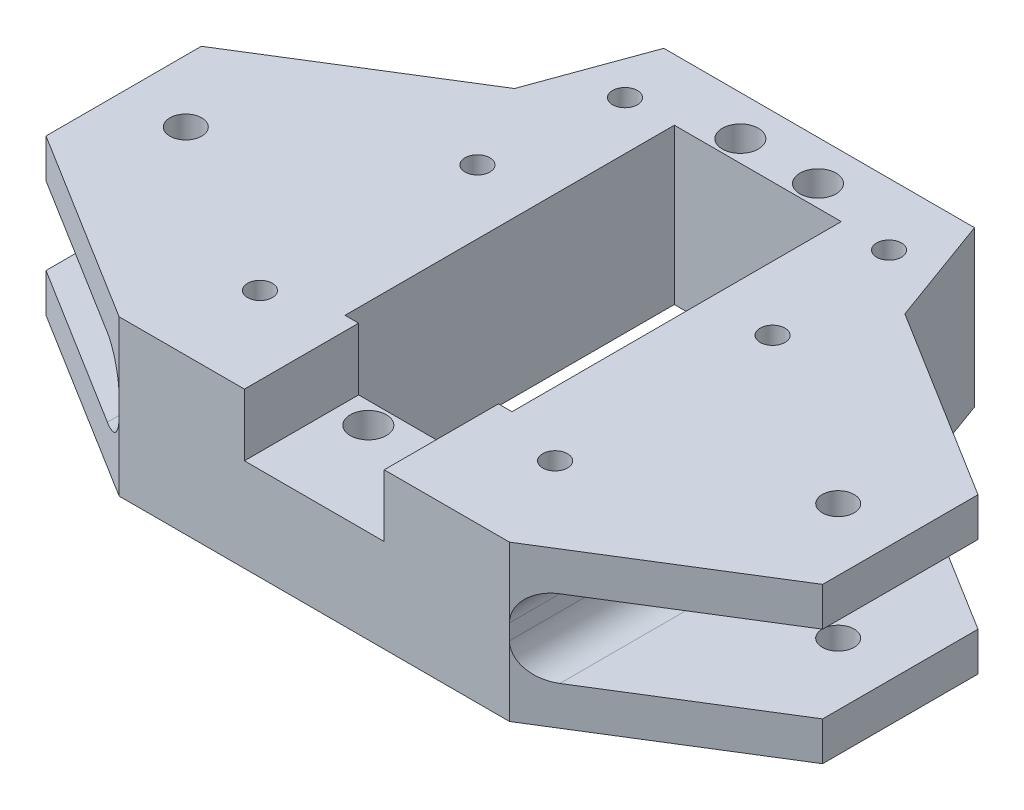
SolidWorks part; units mm, degrees
ref_plane "Front Plane" through (0, 0, 0) normal (0, 0, 1) x (1, 0, 0)
ref_plane "Top Plane" through (0, 0, 0) normal (0, 1, 0) x (1, 0, 0)
ref_plane "Right Plane" through (0, 0, 0) normal (1, 0, 0) x (0, 0, -1)
sketch "Sketch1" plane through (0, 0, 0) normal (0, 1, 0) x (1, 0, 0)
  line L0 (0, 0) -> (0, 55585.7092) construction
  line L1 (0, 0) -> (55585.7092, 0) construction
  line L2 (20, 39.5477) -> (-20, 39.5477)
  line L3 (-20, 39.5477) -> (-25.1303, 25.4523)
  line L4 (-25.1303, 25.4523) -> (-50, 10)
  line L5 (-50, 10) -> (-50, -10)
  line L11 (50, 10) -> (50, -10)
  line L12 (25.1303, 25.4523) -> (50, 10)
  line L13 (20, 39.5477) -> (25.1303, 25.4523)
  line L14 (25.1303, -25.4523) -> (50, -10)
  line L15 (-25.1303, -25.4523) -> (-50, -10)
  line L19 (25.1303, -25.4523) -> (-25.1303, -25.4523)
  point P7 (50, 0)
  point P12 (-50, 0)
  point P14 (0, -10.7407)
  point P19 (0, 39.5477)
  dimension "D1" = 40
  dimension "D2" = 20
  dimension "D3" = 65
  dimension "D4" = 100
  dimension "D5" = 110
  dimension "D8" = 15
extrude "Main-Body" add sketch "Sketch1" along normal mid plane 20
sketch "Sketch2" plane through (0, 10, 0) normal (0, 1, 0) x (1, 0, 0)
  line L0 (0, 47.5477) -> (0, -49952.4523) construction
  line L1 (-50, 0) -> (49950, 0) construction
  line L2 (20, 39.5477) -> (-20, 39.5477) construction
  line L3 (-10, 10.45) -> (10, 10.45) construction
  line L4 (10, -10) -> (-10, -10) construction
  line L5 (-10, -10) -> (-10, 30.9) construction
  line L6 (-10, 30.9) -> (10, 30.9) construction
  line L7 (10, -10) -> (10, 30.9) construction
  line L8 (0, -25.4523) -> (50000, -25.4523) construction
  line L9 (-50, 10) -> (-50, -10) construction
  line L10 (-5, 34.4) -> (5, 34.4) construction
  line L11 (-5, -13.5) -> (5, -13.5) construction
  line L12 (-25.1303, -25.4523) -> (25.1303, -25.4523) construction
  line L14 (-10.75, 31.65) -> (10.75, 31.65)
  line L15 (-10.75, 31.65) -> (-10.75, -10.75)
  line L16 (-10.75, -10.75) -> (10.75, -10.75)
  line L17 (10.75, 31.65) -> (10.75, -10.75)
  line L18 (-10.75, 31.65) -> (10.75, -10.75) construction
  line L19 (-10.75, -10.75) -> (10.75, 31.65) construction
  circle A0 centre (-5, -13.5) radius 2.325
  circle A1 centre (5, -13.5) radius 2.325
  circle A2 centre (-5, 34.4) radius 2.325
  circle A3 centre (5, 34.4) radius 2.325
  circle A4 centre (0, 0) radius 2 construction
  circle A5 centre (-42, 0) radius 2.05
  circle A6 centre (42, 0) radius 2.05
  point P22 (0, -10)
  point P23 (0, 30.9)
  point P28 (0, 39.5477)
  point P29 (0, -13.5)
  point P30 (0, 34.4)
  point P31 (-50, 0)
  point P32 (0, 10.45)
  dimension "D1" = 4.65
  dimension "D4" = 4.65
  dimension "D10" = 4.65
  dimension "D11" = 4.65
  dimension "D13" = 4
  dimension "D16" = 4.1
  dimension "D3" = 10
  dimension "D6" = 10
  dimension "D7" = 20
  dimension "D8" = 3.5
  dimension "D9" = 3.5
  dimension "D5" = 40.9
  dimension "D2" = 0.75
  dimension "D12" = 0.75
  dimension "D14" = 10
  dimension "D15" = 0
  dimension "D17" = 8
extrude "Servo&RotRod-Cutout" cut sketch "Sketch2" against normal blind 30
sketch "Sketch3" plane through (0, 0, 25.4523) normal (0, 0, 1) x (1, 0, 0)
  line L0 (0, 0) -> (0, 50000) construction
  line L1 (0, 0) -> (48695.3801, 0) construction
  line L3 (9, 10) -> (-9, 10)
  line L4 (-9, 10) -> (-9, 2)
  line L5 (-9, 2) -> (9, 2)
  line L6 (9, 10) -> (9, 2)
  line L7 (-25.1303, 10) -> (25.1303, 10) construction
  point P10 (0, 0)
  point P11 (0, 10)
  dimension "D1" = 18
  dimension "D2" = 8
  dimension "D3" = 0
extrude "Servo-Cable-Cutout" cut sketch "Sketch3" against normal up to surface (57.1023 mm away)
sketch "Sketch4" plane through (0, 0, 25.4523) normal (0, 0, 1) x (1, 0, 0)
  line L0 (0, 0) -> (0, 50000) construction
  line L1 (50, 0) -> (50050, 0) construction
  line L2 (50, 10) -> (50, -10) construction
  line L3 (-50, -5) -> (-50, 5)
  line L4 (-50, 10) -> (-50, -10) construction
  line L5 (-50, 5) -> (-25.1303, 5)
  line L6 (-25.1303, 5) -> (-25.1303, -5)
  line L7 (-50, -5) -> (-25.1303, -5)
  line L10 (-25.1303, 10) -> (-25.1303, -10) construction
  point P7 (50, 0)
  point P15 (-25.1303, 0)
  point P16 (-50, 0)
  dimension "D1" = 0
  dimension "D2" = 10
extrude "Control-Arm-Cutout" cut sketch "Sketch4" against normal through all both and the other way through all
mirror "Mirror1" about plane through (0, 0, 0) normal (1, 0, 0) of "Control-Arm-Cutout"
sketch "Sketch5" plane through (0, 10, 0) normal (0, 1, 0) x (1, 0, 0)
  line L0 (-50, 0) -> (49950, 0) construction
  line L1 (-50, 10) -> (-50, -10) construction
  line L2 (0, 0) -> (0, 50000) construction
  circle A0 centre (-40, 0) radius 2.05
  point P4 (-50, 0)
  dimension "D1" = 4.1
  dimension "D2" = 10
extrude "Cut-Extrude4" [suppressed] cut sketch "Sketch5" against normal through all both and the other way through all
mirror "Mirror2" [suppressed] about plane through (0, 0, 0) normal (1, 0, 0)
fillet "Fillet1" radius 4 4 edges at (-25.1303, -5, 0) (-25.1303, 5, 0) (25.1303, -5, 0) (25.1303, 5, 0)
sketch "Sketch6" plane through (0, -10, 0) normal (0, -1, 0) x (1, 0, 0)
  line L0 (0, 0) -> (0, -50000) construction
  line L1 (19, -12.4414) -> (19, -50012.4414) construction
  line L2 (-25.1303, 25.4523) -> (25.1303, 25.4523) construction
  line L3 (20, -39.5477) -> (-20, -39.5477) construction
  circle A0 centre (19, -14.5477) radius 1.6
  circle A1 centre (19, 13.4523) radius 1.6
  circle A2 centre (17, -31.5477) radius 1.6
  circle A3 centre (-17, -31.5477) radius 1.6
  circle A4 centre (-19, 13.4523) radius 1.6
  circle A5 centre (-19, -14.5477) radius 1.6
  dimension "D2" = 3.2
  dimension "D3" = 3.2
  dimension "D7" = 3.2
  dimension "D1" = 19
  dimension "D4" = 12
  dimension "D5" = 25
  dimension "D6" = 17
  dimension "D8" = 8
extrude "Mount-Holes-Chassis" cut sketch "Sketch6" against normal through all
sketch "Sketch7" plane through (0, -10, 0) normal (0, -1, 0) x (1, 0, 0)
  line L0 (0, 0) -> (0, -50000) construction
  circle A0 centre (17, -31.5477) radius 3.25
  circle A1 centre (19, -14.5477) radius 3.25
  circle A2 centre (19, 13.4523) radius 3.25
  circle A3 centre (-19, 13.4523) radius 3.25
  circle A4 centre (-19, -14.5477) radius 3.25
  circle A5 centre (-17, -31.5477) radius 3.25
  dimension "D1" = 6.5
  dimension "D2" = 6.5
  dimension "D3" = 6.5
extrude "Bolt-Head-Holes" cut sketch "Sketch7" against normal blind 4.5
equation "\"D10@Sketch2\"=\"D1@Sketch2\""
equation "\"D11@Sketch2\"=\"D1@Sketch2\""
equation "\"D3@Sketch6\"=\"D2@Sketch6\""
equation "\"D7@Sketch6\"=\"D2@Sketch6\""
equation "\"D2@Sketch7\"=\"D1@Sketch7\""
equation "\"D3@Sketch7\"=\"D1@Sketch7\""
